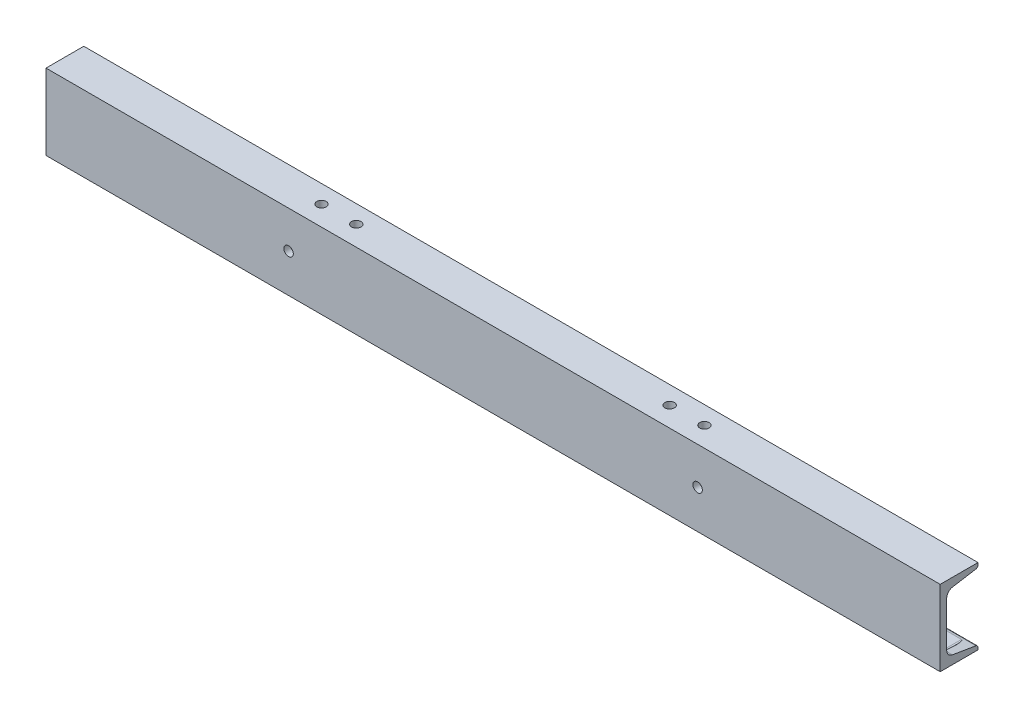
SolidWorks part; units mm, degrees
material "Plain Carbon Steel"
ref_plane "Front Plane" through (0, 0, 0) normal (0, 0, 1) x (1, 0, 0)
ref_plane "Top Plane" through (0, 0, 0) normal (0, 1, 0) x (1, 0, 0)
ref_plane "Right Plane" through (0, 0, 0) normal (1, 0, 0) x (0, 0, -1)
sketch "Sketch1" plane through (0, 0, 0) normal (0, 1, 0) x (1, 0, 0)
  line L0 (-450, 0) -> (450, 0)
  dimension "D1" = 900
other "Structural Member1"
ref_plane "Plane1" through (-450, 0, 0) normal (1, 0, 0) x (0, 0, -1)
sketch "Sketch11" plane through (-450, 0, 0) normal (1, 0, 0) x (0, 0, -1)
  line L0 (0, -38.1) -> (0, 38.1)
  line L1 (0, 38.1) -> (38.0492, 38.1)
  line L2 (0, -38.1) -> (38.0492, -38.1)
  line L5 (31.75, -31.1658) -> (6.35, -31.1658) construction
  line L6 (0, 0) -> (6.5532, 0) construction
  line L12 (6.5532, 22.7314) -> (6.5532, -22.7314)
  line L15 (38.0492, 38.1) -> (38.0492, 35.9423)
  line L16 (38.0492, -38.1) -> (38.0492, -35.9423)
  line L17 (12.2837, 29.4961) -> (35.9268, 33.4369)
  line L18 (12.2837, -29.4961) -> (35.9268, -33.4369)
  arc A9 (6.5532, -22.7314) -> (12.2837, -29.4961) centre (13.4112, -22.7314) ccw
  arc A10 (6.5532, 22.7314) -> (12.2837, 29.4961) centre (13.4112, 22.7314) cw
  arc A11 (38.0492, 35.9423) -> (35.9268, 33.4369) centre (35.5092, 35.9423) cw
  arc A12 (38.0492, -35.9423) -> (35.9268, -33.4369) centre (35.5092, -35.9423) ccw
  point P4 (38.0492, 33.7907)
  point P5 (38.0492, -33.7907)
  point P6 (3.2766, 0)
  point P7 (19.0246, 38.1)
  point P12 (19.0246, -38.1)
  point P13 (0, 0)
  dimension "RI" = 6.858
  dimension "D2" = 9.463
  dimension "RA" = 2.54
  dimension "Depth" = 76.2
  dimension "BF" = 38.0492
  dimension "TW" = 6.5532
  dimension "flange" = 2.1577
  dimension "TF" = 6.9342
sketch "Sketch12" plane through (0, 0, 0) normal (0, 1, 0) x (1, 0, 0)
  line L0 (-412.5239, 20) -> (413.742, 20) construction
  line L1 (-450, 0) -> (450, 0) construction
  line L2 (0, 0) -> (0, 45.9021) construction
  line L3 (-450, 38.0492) -> (-450, 0) construction
  circle A0 centre (-425, 20) radius 4.7625
  circle A1 centre (425, 20) radius 4.7625
  dimension "D2" = 9.525
  dimension "D1" = 20
  dimension "D3" = 25
extrude "Cut-Extrude1" cut sketch "Sketch12" against normal through all
sketch "Sketch15" plane through (0, 0, -6.5532) normal (0, 0, -1) x (-1, 0, 0)
  line L0 (-425, -21.1359) -> (-425, -40.4286) construction
  line L1 (-375.1366, -28.1) -> (-474.8634, -28.1) construction
  line L2 (-450, -38.1) -> (450, -38.1) construction
  line L3 (-412.5, -28.1) -> (-437.5, -28.1) construction
  line L4 (-412.5, -33.1) -> (-437.5, -33.1)
  line L5 (-412.5, -23.1) -> (-437.5, -23.1)
  line L6 (0, 0) -> (0, -58.1771) construction
  line L7 (412.5, -28.1) -> (437.5, -28.1) construction
  line L8 (412.5, -33.1) -> (437.5, -33.1)
  line L9 (412.5, -23.1) -> (437.5, -23.1)
  arc A0 (-412.5, -33.1) -> (-412.5, -23.1) centre (-412.5, -28.1) ccw
  arc A1 (-437.5, -23.1) -> (-437.5, -33.1) centre (-437.5, -28.1) ccw
  arc A2 (412.5, -33.1) -> (412.5, -23.1) centre (412.5, -28.1) cw
  arc A3 (437.5, -23.1) -> (437.5, -33.1) centre (437.5, -28.1) cw
  ellipse E0 centre (-425, -30.7822) end of major axis (-429.7625, -30.7822) minor radius 0.7938 construction
  point P0 (-425, -30.7822)
  point P11 (-425, -28.1)
  point P16 (-425, -28.1)
  point P26 (425, -28.1)
  dimension "D2" = 5
  dimension "D1" = 10
  dimension "D3" = 25
extrude "Cut-Extrude2" cut sketch "Sketch15" along normal blind 40
sketch "Sketch16" plane through (0, 0, 0) normal (0, 1, 0) x (1, 0, 0)
  line L0 (0, -46.4014) -> (0, 86.4014) construction
  line L1 (-394.0256, 20) -> (394.0256, 20) construction
  line L2 (450, 0) -> (-450, 0) construction
  circle A0 centre (-192.7, 20) radius 4.7625
  circle A1 centre (-157.7, 20) radius 4.7625
  circle A2 centre (157.7, 20) radius 4.7625
  circle A3 centre (192.7, 20) radius 4.7625
  point P5 (0, 20)
  point P6 (0, 20)
  dimension "D2" = 9.525
  dimension "D1" = 20
  dimension "D3" = 192.7
  dimension "D4" = 35
extrude "Cut-Extrude3" cut sketch "Sketch16" along normal through all
sketch "Sketch17" plane through (0, 0, 0) normal (0, 0, 1) x (1, 0, 0)
  circle A0 centre (205.8375, 0.6) radius 4.7625 construction
  circle A1 centre (-205.8375, 0.6) radius 4.7625 construction
  circle A2 centre (205.8375, 0.6) radius 4.7625
  circle A3 centre (-205.8375, 0.6) radius 4.7625
extrude "Cut-Extrude4" cut sketch "Sketch17" against normal through all
